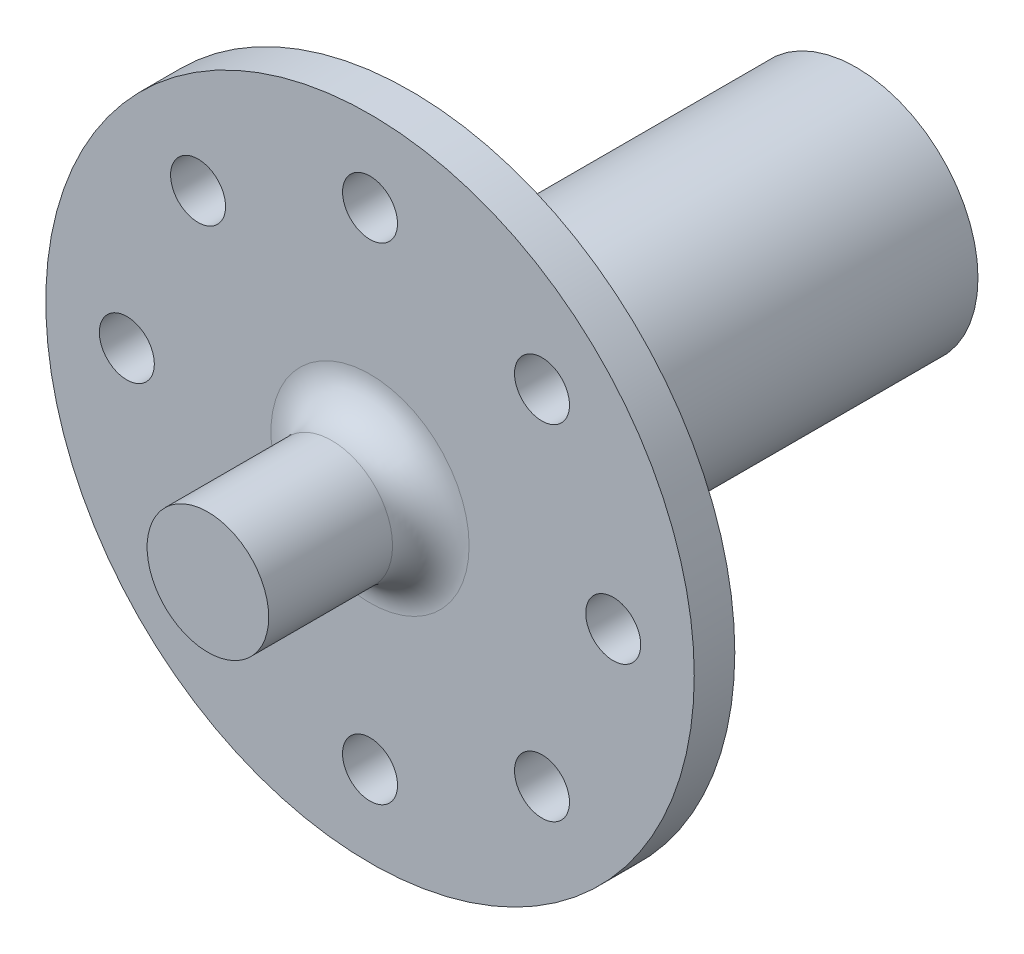
SolidWorks part; units mm, degrees
ref_plane "Front Plane" through (0, 0, 0) normal (0, 0, 1) x (1, 0, 0)
ref_plane "Top Plane" through (0, 0, 0) normal (0, 1, 0) x (1, 0, 0)
ref_plane "Right Plane" through (0, 0, 0) normal (1, 0, 0) x (0, 0, -1)
sketch "Sketch1" plane through (0, 0, 0) normal (0, 0, 1) x (1, 0, 0)
  circle A1 centre (0, 0) radius 9.525
  dimension "D4" = 19.05
extrude "Boss-Extrude1" add sketch "Sketch1" along normal blind 34.925
sketch "Sketch2" plane through (0, 0, 34.925) normal (0, 0, 1) x (1, 0, 0)
  circle A1 centre (0, 0) radius 25.4
  dimension "D1" = 50.8
extrude "Boss-Extrude2" add sketch "Sketch2" along normal blind 3.175
sketch "Sketch3" plane through (0, 0, 38.1) normal (0, 0, 1) x (1, 0, 0)
  circle A1 centre (0, 0) radius 4.7625
  dimension "D1" = 9.525
extrude "Boss-Extrude3" add sketch "Sketch3" along normal blind 12.7
sketch "Sketch4" plane through (0, 0, 38.1) normal (0, 0, 1) x (1, 0, 0)
  line L0 (0, 0) -> (0, 34.5092) construction
  circle A2 centre (0, 19.05) radius 2.1526
  point P10 (0, 0)
  point P14 (0, 0)
  point P19 (0, 19.05)
  dimension "D1" = 19.05
  dimension "D3" = 4.3053
extrude "Cut-Extrude1" cut sketch "Sketch4" against normal blind 19.05
pattern_circular "CirPattern1" count 8 over 360 about axis through (0, 0, 0) along (0, 0, 1) of "Cut-Extrude1"
fillet "Fillet1" radius 3 1 edges at (4.7625, 0, 38.1)
sketch "Sketch5" plane through (0, 0, 0) normal (0, 0, -1) x (-1, 0, 0)
  line L0 (-1.5, 5.2) -> (1.5, 5.2)
  line L1 (-1.5, 5.2) -> (-1.5, 3.7081)
  line L2 (1.5, 5.2) -> (1.5, 3.7081)
  arc A0 (-1.5, 3.7081) -> (1.5, 3.7081) centre (0, 0) ccw
  point P5 (0, 5.2)
  point P6 (0, -4)
  dimension "D1" = 8
  dimension "D2" = 3
  dimension "D3" = 9.2
extrude "16.6mmForKeywayDepthand.6mmForExtra.375" cut sketch "Sketch5" against normal blind 17.15
